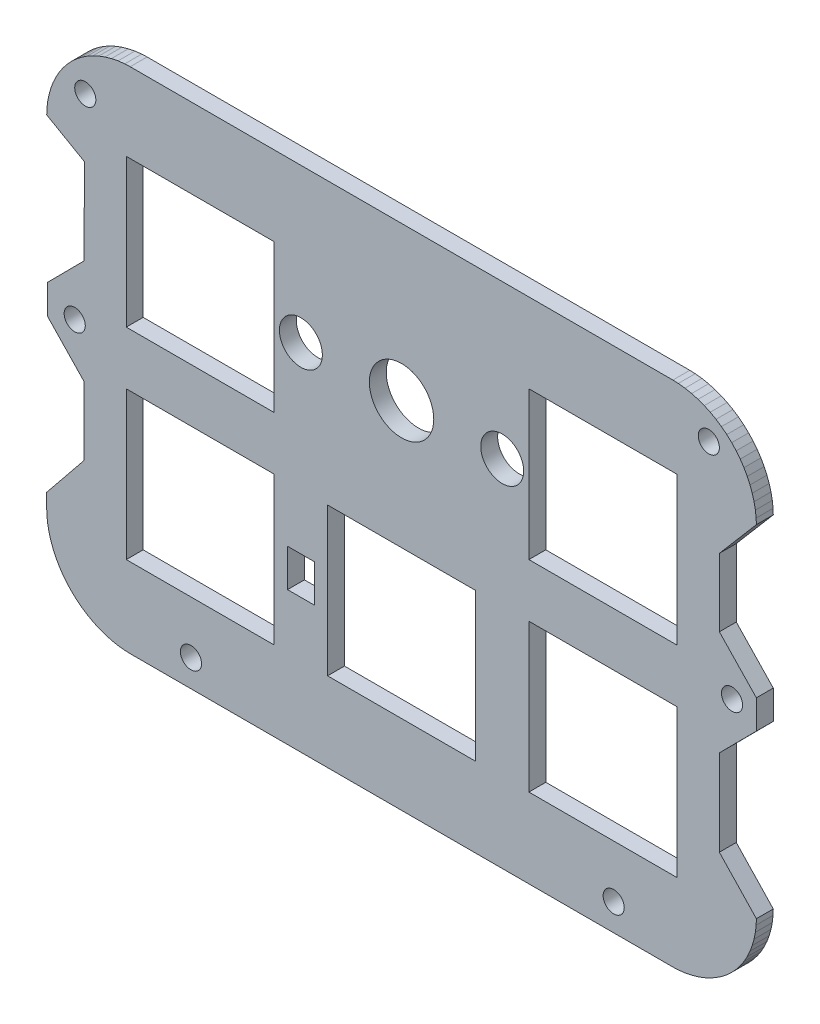
SolidWorks part; units mm, degrees
ref_plane "Front Plane" through (0, 0, 0) normal (0, 0, 1) x (1, 0, 0)
ref_plane "Top Plane" through (0, 0, 0) normal (0, 1, 0) x (1, 0, 0)
ref_plane "Right Plane" through (0, 0, 0) normal (1, 0, 0) x (0, 0, -1)
sketch "Model" plane through (0, 0, 0) normal (0, 0, 1) x (1, 0, 0)
  line L0 (16.6205, 16.7817) -> (2.621, 16.7817)
  line L1 (2.621, 16.7817) -> (2.621, 2.7823)
  line L2 (2.621, 2.7823) -> (16.6205, 2.7823)
  line L3 (16.6205, 2.7823) -> (16.6205, 16.7817)
  line L4 (54.7204, 35.8316) -> (40.7211, 35.8316)
  line L5 (40.7211, 35.8316) -> (40.7211, 21.8323)
  line L6 (40.7211, 21.8323) -> (54.7204, 21.8323)
  line L7 (54.7204, 21.8323) -> (54.7204, 35.8316)
  line L8 (21.671, 16.7817) -> (21.671, 2.7823)
  line L9 (21.671, 2.7823) -> (35.6704, 2.7823)
  line L10 (35.6704, 2.7823) -> (35.6704, 16.7817)
  line L11 (35.6704, 16.7817) -> (21.671, 16.7817)
  line L12 (16.6205, 21.8323) -> (16.6205, 35.8316)
  line L13 (16.6205, 35.8316) -> (2.621, 35.8316)
  line L14 (2.621, 35.8316) -> (2.621, 21.8323)
  line L15 (2.621, 21.8323) -> (16.6205, 21.8323)
  line L16 (40.7211, 16.7817) -> (40.7211, 2.7823)
  line L17 (40.7211, 2.7823) -> (54.7204, 2.7823)
  line L18 (54.7204, 2.7823) -> (54.7204, 16.7817)
  line L19 (54.7204, 16.7817) -> (40.7211, 16.7817)
  line L20 (17.8815, 7.9506) -> (20.4215, 7.9506)
  line L21 (20.4215, 7.9506) -> (20.4215, 11.5066)
  line L22 (20.4215, 11.5066) -> (17.8815, 11.5066)
  line L23 (17.8815, 11.5066) -> (17.8815, 7.9506)
  line L24 (-4.8839, 35.9739) -> (-4.8132, 36.606)
  line L25 (-4.8132, 36.606) -> (-4.6861, 37.2302)
  line L26 (-4.6861, 37.2302) -> (-4.5165, 37.8379)
  line L27 (-4.5165, 37.8379) -> (-4.2958, 38.4262)
  line L28 (-4.2958, 38.4262) -> (-4.0404, 38.9843)
  line L29 (-4.0404, 38.9843) -> (-3.7347, 39.5306)
  line L30 (-3.7347, 39.5306) -> (-3.3855, 40.0581)
  line L31 (-3.3855, 40.0581) -> (-2.9914, 40.5561)
  line L32 (-2.9914, 40.5561) -> (-2.5647, 41.0193)
  line L33 (-2.5647, 41.0193) -> (-2.1021, 41.445)
  line L34 (-2.1021, 41.445) -> (-1.6071, 41.8367)
  line L35 (-1.6071, 41.8367) -> (-1.0799, 42.1864)
  line L36 (-1.0799, 42.1864) -> (-0.5311, 42.4935)
  line L37 (-0.5311, 42.4935) -> (0.0278, 42.7492)
  line L38 (0.0278, 42.7492) -> (0.6153, 42.9693)
  line L39 (0.6153, 42.9693) -> (1.2219, 43.1387)
  line L40 (1.2219, 43.1387) -> (1.8475, 43.2662)
  line L41 (1.8475, 43.2662) -> (2.4814, 43.3368)
  line L42 (2.4814, 43.3368) -> (2.9943, 43.3575)
  line L43 (2.9943, 43.3575) -> (54.3453, 43.3575)
  line L44 (54.3453, 43.3575) -> (54.8614, 43.3368)
  line L45 (54.8614, 43.3368) -> (55.4918, 43.2662)
  line L46 (55.4918, 43.2662) -> (56.1176, 43.1393)
  line L47 (56.1176, 43.1393) -> (56.7265, 42.9691)
  line L48 (56.7265, 42.9691) -> (57.3126, 42.7496)
  line L49 (57.3126, 42.7496) -> (57.8785, 42.491)
  line L50 (57.8785, 42.491) -> (58.4255, 42.1827)
  line L51 (58.4255, 42.1827) -> (58.94, 41.8416)
  line L52 (58.94, 41.8416) -> (59.4458, 41.4441)
  line L53 (59.4458, 41.4441) -> (59.9121, 41.0114)
  line L54 (59.9121, 41.0114) -> (60.3321, 40.5554)
  line L55 (60.3321, 40.5554) -> (60.7161, 40.0699)
  line L56 (60.7161, 40.0699) -> (61.0691, 39.5438)
  line L57 (61.0691, 39.5438) -> (61.383, 38.9827)
  line L58 (61.383, 38.9827) -> (61.6444, 38.4106)
  line L59 (61.6444, 38.4106) -> (61.8551, 37.8381)
  line L60 (61.8551, 37.8381) -> (62.0283, 37.2326)
  line L61 (62.0283, 37.2326) -> (62.1523, 36.6056)
  line L62 (62.1523, 36.6056) -> (62.225, 35.9862)
  line L63 (62.225, 35.9862) -> (62.2463, 35.4586)
  line L64 (62.2453, 3.1661) -> (62.2262, 2.6367)
  line L65 (62.2262, 2.6367) -> (62.1524, 2.0114)
  line L66 (62.1524, 2.0114) -> (62.0292, 1.3849)
  line L67 (62.0292, 1.3849) -> (61.8553, 0.7766)
  line L68 (61.8553, 0.7766) -> (61.6442, 0.2027)
  line L69 (61.6442, 0.2027) -> (61.3794, -0.3764)
  line L70 (61.3794, -0.3764) -> (61.0647, -0.9348)
  line L71 (61.0647, -0.9348) -> (60.7212, -1.4467)
  line L72 (60.7212, -1.4467) -> (60.333, -1.9414)
  line L73 (60.333, -1.9414) -> (59.9058, -2.4019)
  line L74 (59.9058, -2.4019) -> (59.4459, -2.8288)
  line L75 (59.4459, -2.8288) -> (58.9476, -3.2204)
  line L76 (58.9476, -3.2204) -> (58.4345, -3.5634)
  line L77 (58.4345, -3.5634) -> (57.8802, -3.876)
  line L78 (57.8802, -3.876) -> (57.3021, -4.1405)
  line L79 (57.3021, -4.1405) -> (56.7262, -4.3529)
  line L80 (56.7262, -4.3529) -> (56.116, -4.5268)
  line L81 (56.116, -4.5268) -> (55.4922, -4.6494)
  line L82 (55.4922, -4.6494) -> (54.8784, -4.7221)
  line L83 (54.8784, -4.7221) -> (54.3469, -4.7437)
  line L84 (54.3469, -4.7437) -> (2.9928, -4.7437)
  line L85 (2.9928, -4.7437) -> (2.4645, -4.7221)
  line L86 (2.4645, -4.7221) -> (1.8472, -4.6494)
  line L87 (1.8472, -4.6494) -> (1.2235, -4.5262)
  line L88 (1.2235, -4.5262) -> (0.6156, -4.353)
  line L89 (0.6156, -4.353) -> (0.0383, -4.1402)
  line L90 (0.0383, -4.1402) -> (-0.5328, -3.8785)
  line L91 (-0.5328, -3.8785) -> (-1.0889, -3.5671)
  line L92 (-1.0889, -3.5671) -> (-1.6146, -3.2154)
  line L93 (-1.6146, -3.2154) -> (-2.1023, -2.8297)
  line L94 (-2.1023, -2.8297) -> (-2.5583, -2.4098)
  line L95 (-2.5583, -2.4098) -> (-2.9923, -1.9422)
  line L96 (-2.9923, -1.9422) -> (-3.3906, -1.4349)
  line L97 (-3.3906, -1.4349) -> (-3.7304, -0.9216)
  line L98 (-3.7304, -0.9216) -> (-4.0368, -0.378)
  line L99 (-4.0368, -0.378) -> (-4.2957, 0.1871)
  line L100 (-4.2957, 0.1871) -> (-4.5168, 0.7768)
  line L101 (-4.5168, 0.7768) -> (-4.6871, 1.3875)
  line L102 (-4.6871, 1.3875) -> (-4.8133, 2.0111)
  line L103 (-4.8133, 2.0111) -> (-4.8839, 2.6392)
  line L104 (-4.8839, 2.6392) -> (-4.9049, 3.156)
  line L105 (-4.9049, 3.156) -> (-4.9049, 4.5385)
  line L106 (-4.9049, 35.4602) -> (-4.8839, 35.9739)
  line L107 (62.2459, 21.2672) -> (58.746, 24.9291)
  line L108 (62.2463, 35.4586) -> (58.7462, 31.3582)
  line L109 (62.2456, 18.5347) -> (58.7457, 15.0073)
  line L110 (62.2453, 3.1661) -> (58.7454, 6.8644)
  line L111 (62.2459, 21.2672) -> (62.2456, 18.5347)
  line L112 (58.7462, 31.3582) -> (58.746, 24.9291)
  line L113 (58.7457, 15.0073) -> (58.7454, 6.8644)
  line L114 (-1.354, 8.9291) -> (-1.3536, 15.3581)
  line L115 (-4.9049, 4.5385) -> (-1.354, 8.9291)
  line L116 (-4.8537, 19.0201) -> (-1.3536, 15.3581)
  line L117 (-4.8537, 19.0201) -> (-4.8534, 21.7526)
  line L118 (-4.8534, 21.7526) -> (-1.3535, 25.2801)
  line L119 (-1.3535, 25.2801) -> (-1.3533, 33.4229)
  line L120 (-1.3533, 33.4229) -> (-4.9049, 35.4602)
  circle A0 centre (38.1958, 28.832) radius 2.032
  circle A1 centre (19.1458, 28.832) radius 2.032
  circle A2 centre (28.6708, 28.832) radius 3.048
  circle A3 centre (-2.2555, 20.0102) radius 1
  circle A4 centre (-1.2555, 39.0102) radius 1
  circle A5 centre (57.7445, 40.0102) radius 1
  circle A6 centre (59.9445, 20.0102) radius 1
  circle A7 centre (8.7445, -2.1898) radius 1
  circle A8 centre (48.7445, -2.1898) radius 1
extrude "凸台-拉伸1" add sketch "Model" along normal blind 1.6
